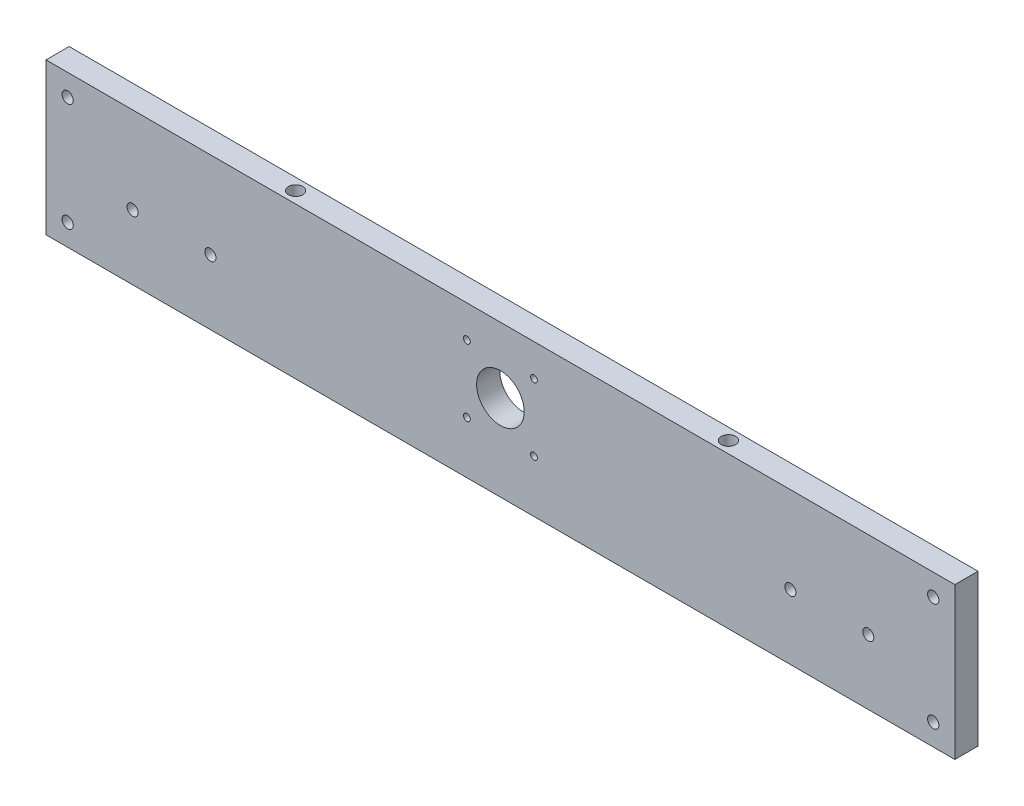
SolidWorks part; units mm, degrees
ref_plane "Plano frontal" through (0, 0, 0) normal (0, 0, 1) x (1, 0, 0)
ref_plane "Plano superior" through (0, 0, 0) normal (0, 1, 0) x (1, 0, 0)
ref_plane "Plano direito" through (0, 0, 0) normal (1, 0, 0) x (0, 0, -1)
sketch "Esboço1" plane through (0, 0, 0) normal (0, 0, 1) x (1, 0, 0)
  line L1 (210, -35) -> (-210, -35)
  line L2 (210, -35) -> (210, 35)
  line L3 (210, 35) -> (-210, 35)
  line L4 (-210, -35) -> (-210, 35)
  line L5 (210, -35) -> (-210, 35) construction
  line L6 (210, 35) -> (-210, -35) construction
  point P0 (0, 0)
  dimension "D1" = 70
  dimension "D2" = 420
extrude "Ressalto-extrusão1" add sketch "Esboço1" along normal blind 10.7
sketch "Esboço4" plane through (0, 0, 10.7) normal (0, 0, 1) x (1, 0, 0)
  line L0 (0, -41.8048) -> (0, 51.6718) construction
  line L1 (-210, -35) -> (210, -35) construction
  line L2 (17.6554, 4.65) -> (-17.9019, 4.65) construction
  circle A0 centre (0, 4.65) radius 11
  dimension "D1" = 22
  dimension "D2" = 39.65
extrude "Corte-extrusão3" cut sketch "Esboço4" against normal through all
hole_wizard "Furo roscado para conduíte de #10-321" positions "Esboço5" profile "Esboço6" tap size "#10-32" standard "Helicoil® Inch" end condition through all
sketch "Esboço5" plane through (0, 0, 10.7) normal (0, 0, 1) x (1, 0, 0)
  line L0 (-210, 35) -> (-210, -35) construction
  line L1 (-210, -35) -> (210, -35) construction
  line L2 (0, 0) -> (0, 58.7943) construction
  point P0 (-170, -5)
  point P2 (-134, -5)
  point P15 (134, -5)
  point P16 (170, -5)
  dimension "D1" = 40
  dimension "D2" = 36
  dimension "D3" = 30
sketch "Esboço6" plane through (-170, -5, 10.7) normal (1, 0, 0) x (0, -1, 0)
  line L0 (0, 0) -> (0, 10.7)
  line L1 (0, 10.7) -> (2.5527, 10.7)
  line L2 (2.5527, 10.7) -> (2.5527, 0)
  line L5 (2.5527, 0) -> (0, 0)
  line L11 (0, -6.35) -> (0, 107.95) construction
  dimension "Thru Tap Drill Dia." = 5.1054
  dimension "Thru Tap Drill Depth" = 10.7
cosmetic thread "Rosca de furo1" parameters "D1"=15, "D2"=5.936
cosmetic thread "Rosca de furo2" parameters "D1"=15, "D2"=5.936
cosmetic thread "Rosca de furo3" parameters "D1"=15, "D2"=5.936
cosmetic thread "Rosca de furo4" parameters "D1"=15, "D2"=5.936
hole_wizard "Furo roscado para conduíte de M5x0.81" positions "Esboço7" profile "Esboço8" tap size "M5x0.8" standard "Helicoil® Metric" end condition through all
sketch "Esboço7" plane through (0, 0, 10.7) normal (0, 0, 1) x (1, 0, 0)
  line L0 (210, 35) -> (-210, 35) construction
  line L1 (-210, 35) -> (-210, -35) construction
  line L2 (0, 0) -> (0, 49.8983) construction
  line L4 (0, 0) -> (52.2601, 0) construction
  point P0 (-200, 25)
  point P18 (-200, -25)
  point P20 (200, -25)
  point P21 (200, 25)
  dimension "D1" = 10
  dimension "D2" = 10
sketch "Esboço8" plane through (-200, 25, 10.7) normal (1, 0, 0) x (0, -1, 0)
  line L0 (0, 0) -> (0, 10.7)
  line L1 (0, 10.7) -> (2.6, 10.7)
  line L2 (2.6, 10.7) -> (2.6, 0)
  line L5 (2.6, 0) -> (0, 0)
  line L11 (0, -6.35) -> (0, 107.95) construction
  dimension "Thru Tap Drill Dia." = 5.2
  dimension "Thru Tap Drill Depth" = 10.7
cosmetic thread "Rosca de furo5" parameters "D1"=15, "D2"=6.145
cosmetic thread "Rosca de furo6" parameters "D1"=15, "D2"=6.145
cosmetic thread "Rosca de furo7" parameters "D1"=15, "D2"=6.145
cosmetic thread "Rosca de furo8" parameters "D1"=15, "D2"=6.145
hole_wizard "Furo roscado para conduíte de M3x0.51" positions "Esboço9" profile "Esboço10" tap size "M3x0.5" standard "Helicoil® Metric" end condition through all
sketch "Esboço9" plane through (0, 0, 10.7) normal (0, 0, 1) x (1, 0, 0)
  line L0 (0, 0) -> (0, 27.4734) construction
  line L3 (0, 4.65) -> (19.1995, 4.65) construction
  circle A0 centre (0, 4.65) radius 11 construction
  point P0 (-15.5, 20.15)
  point P18 (-15.5, -10.85)
  point P20 (15.5, -10.85)
  point P21 (15.5, 20.15)
  dimension "D1" = 15.5
  dimension "D2" = 15.5
sketch "Esboço10" plane through (-15.5, 20.15, 10.7) normal (1, 0, 0) x (0, -1, 0)
  line L0 (0, 0) -> (0, 10.7)
  line L1 (0, 10.7) -> (1.575, 10.7)
  line L2 (1.575, 10.7) -> (1.575, 0)
  line L5 (1.575, 0) -> (0, 0)
  line L11 (0, -6.35) -> (0, 107.95) construction
  dimension "Thru Tap Drill Dia." = 3.15
  dimension "Thru Tap Drill Depth" = 10.7
cosmetic thread "Rosca de furo9" parameters "D1"=15, "D2"=3.716
cosmetic thread "Rosca de furo10" parameters "D1"=15, "D2"=3.716
cosmetic thread "Rosca de furo11" parameters "D1"=15, "D2"=3.716
cosmetic thread "Rosca de furo12" parameters "D1"=15, "D2"=3.716
hole_wizard "Furo roscado para conduíte de 1/4-281" positions "Esboço12" profile "Esboço11" tap size "1/4-28" standard "Helicoil® Inch"
sketch "Esboço12" plane through (0, 35, 0) normal (0, 1, 0) x (1, 0, 0)
  line L0 (0, 0) -> (0, 40.8271) construction
  line L2 (-210, -10.7) -> (-210, 0) construction
  line L4 (-225.1257, -5.35) -> (228.9233, -5.35) construction
  point P0 (-100, -5.35)
  point P17 (100, -5.35)
  dimension "D1" = 110
sketch "Esboço11" plane through (-100, 35, 5.35) normal (1, 0, 0) x (0, 0, 1)
  line L0 (0, 0) -> (0, 16.9917)
  line L1 (0, 16.9917) -> (3.3147, 15)
  line L2 (3.3147, 15) -> (3.3147, 0)
  line L5 (3.3147, 0) -> (0, 0)
  line L10 (0, 16.9917) -> (-3.3147, 15) construction
  line L11 (0, -6.35) -> (0, 107.95) construction
  dimension "Tap Drill Dia." = 6.6294
  dimension "Tap Drill Depth" = 15
  dimension "Drill Angle" = 118
cosmetic thread "Rosca de furo13" parameters "D1"=15, "D2"=7.6073
cosmetic thread "Rosca de furo14" parameters "D1"=15, "D2"=7.6073
